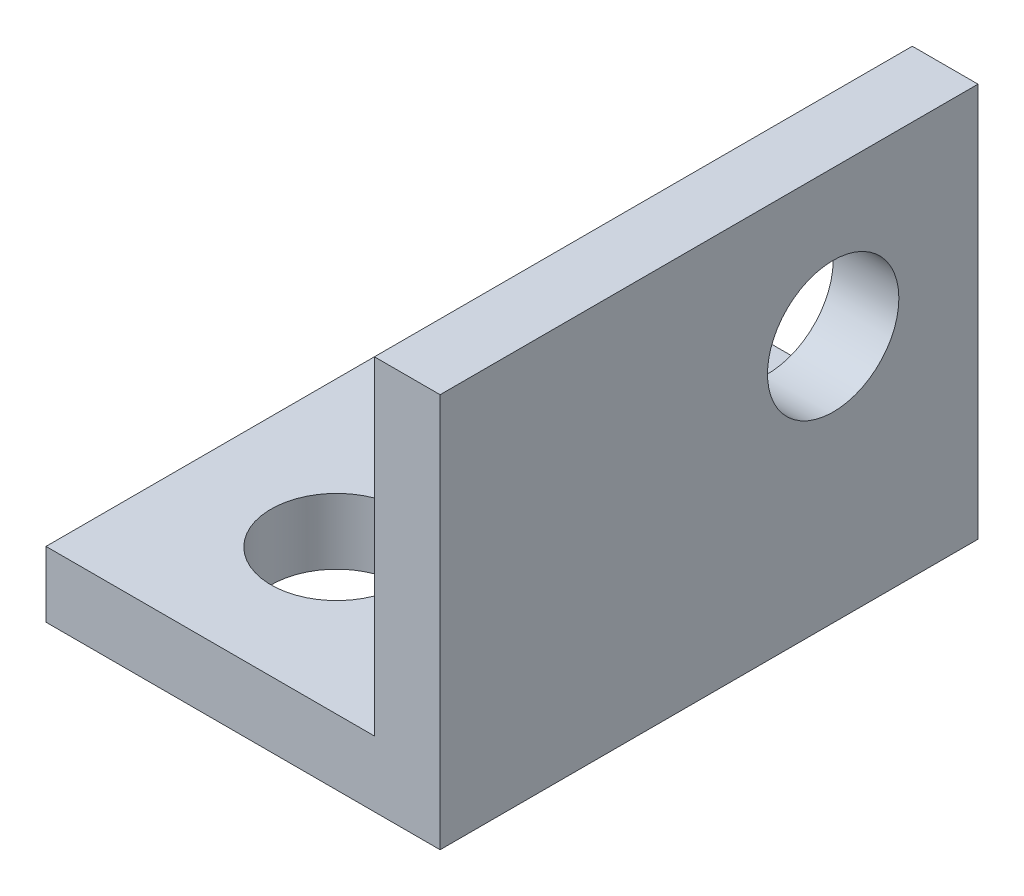
SolidWorks part; units mm, degrees
ref_plane "Front Plane" through (0, 0, 0) normal (0, 0, 1) x (1, 0, 0)
ref_plane "Top Plane" through (0, 0, 0) normal (0, 1, 0) x (1, 0, 0)
ref_plane "Right Plane" through (0, 0, 0) normal (1, 0, 0) x (0, 0, -1)
sketch "Sketch1" plane through (0, 0, 0) normal (0, 0, 1) x (1, 0, 0)
  line L0 (-4.7625, -4.7625) -> (4.7625, -4.7625) construction
  line L1 (4.7625, -4.7625) -> (4.7625, 4.7625) construction
  line L2 (4.7625, 4.7625) -> (3.175, 4.7625) construction
  line L3 (3.175, 4.7625) -> (3.175, -3.175) construction
  line L4 (3.175, -3.175) -> (-4.7625, -3.175) construction
  line L5 (-4.7625, -4.7625) -> (-4.7625, -3.175) construction
  line L6 (3.9688, 4.7625) -> (4.7625, 4.7625) construction
  line L7 (-4.7625, -3.9688) -> (-4.7625, -4.7625) construction
  line L8 (0, 0) -> (4.7625, 0) construction
  line L9 (0, 0) -> (0, -4.7625) construction
  point P3 (0, -4.7625)
  point P5 (3.175, -4.7625)
  point P8 (-4.7625, -4.7625)
  point P12 (-4.7625, -3.175)
  point P17 (3.175, 4.7625)
  dimension "Outside Height" = 9.525
  dimension "Outside Width" = 9.525
  dimension "Wall Thickness" = 1.5875
  dimension "Inside Width" = 7.9375
  dimension "Inside Height" = 7.9375
sketch "Sketch2" [suppressed] plane through (0, 0, 0) normal (1, 0, 0) x (0, 0, -1)
  line L0 (0, 0) -> (609.6, 0) construction
  line L1 (0, 0) -> (-609.6, 0) construction
  line L2 (0, -4.7625) -> (609.6, -4.7625) construction
  line L3 (609.6, -4.7625) -> (609.6, 0) construction
  line L4 (0, -4.7625) -> (-609.6, -4.7625) construction
  line L5 (-609.6, -4.7625) -> (-609.6, 0) construction
  point P3 (600.075, 0)
  point P5 (609.6, 0)
  point P6 (-600.075, 0)
  point P7 (-609.6, 0)
  dimension "D1" = 9.525
  dimension "D2" = 9.525
  dimension "Length" = 1219.2
sketch "Sketch3" plane through (0, 0, 0) normal (0, 0, 1) x (1, 0, 0)
  line L0 (3.175, -3.175) -> (-4.7625, -3.175) construction
  line L1 (-4.7625, -4.7625) -> (-4.7625, -3.175) construction
  line L2 (-4.7625, -4.7625) -> (4.7625, -4.7625) construction
  line L3 (4.7625, -4.7625) -> (4.7625, 4.7625) construction
  line L4 (4.7625, 4.7625) -> (3.175, 4.7625) construction
  line L5 (3.175, 4.7625) -> (3.175, -3.175) construction
  line L6 (3.175, -3.175) -> (-4.7625, -3.175)
  line L7 (-4.7625, -4.7625) -> (-4.7625, -3.175)
  line L8 (-4.7625, -4.7625) -> (4.7625, -4.7625)
  line L9 (4.7625, -4.7625) -> (4.7625, 4.7625)
  line L10 (4.7625, 4.7625) -> (3.175, 4.7625)
  line L11 (3.175, 4.7625) -> (3.175, -3.175)
extrude "Boss-Extrude1" add sketch "Sketch3" along normal mid plane 13
sketch "Sketch4" plane through (4.7625, 0, 0) normal (1, 0, 0) x (0, 0, -1)
  line L0 (-6.5, -4.7625) -> (6.5, -4.7625) construction
  line L3 (6.5, -4.7625) -> (6.5, 4.7625) construction
  circle A0 centre (3, 1.2375) radius 1.5875
  dimension "D1" = 3.175
  dimension "D2" = 6
  dimension "D3" = 3.5
extrude "Cut-Extrude1" cut sketch "Sketch4" against normal blind 10
sketch "Sketch5" plane through (0, -4.7625, 0) normal (0, -1, 0) x (1, 0, 0)
  line L0 (4.7625, 6.5) -> (4.7625, -6.5) construction
  line L2 (-4.7625, 6.5) -> (4.7625, 6.5) construction
  circle A0 centre (-1.2375, 3) radius 1.5875
  dimension "D1" = 3.175
  dimension "D2" = 6
  dimension "D3" = 3.5
extrude "Cut-Extrude2" cut sketch "Sketch5" against normal blind 10
equation "\"D2@Sketch2\"=\"D1@Sketch2\""
equation "\"D1@Sketch2\"=\"outside height@sketch1\""
